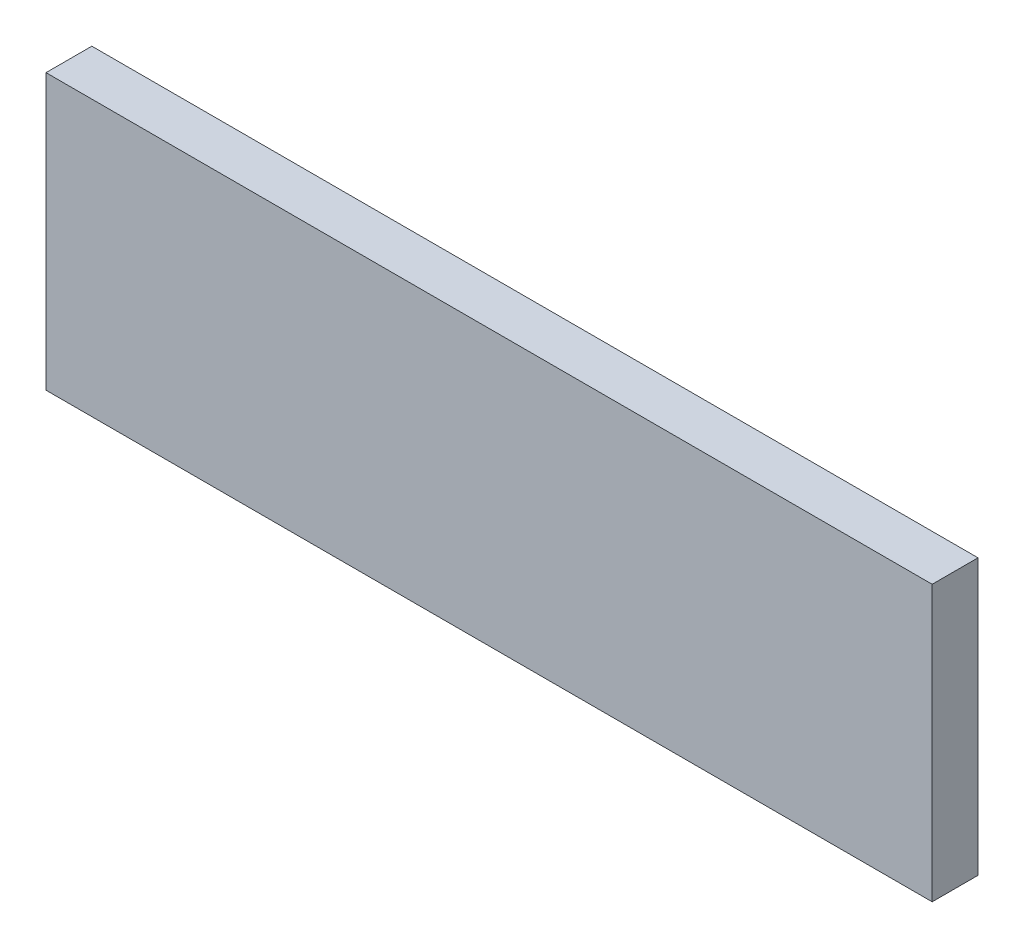
SolidWorks part; units mm, degrees
material "Pine"
ref_plane "Front" through (0, 0, 0) normal (0, 0, 1) x (1, 0, 0)
ref_plane "Top" through (0, 0, 0) normal (0, 1, 0) x (1, 0, 0)
ref_plane "Right" through (0, 0, 0) normal (1, 0, 0) x (0, 0, -1)
sketch "Sketch1" plane through (0, 0, 0) normal (1, 0, 0) x (0, 0, -1)
  line L1 (-9.525, -57.15) -> (9.525, -57.15)
  line L2 (-9.525, -57.15) -> (-9.525, 57.15)
  line L3 (-9.525, 57.15) -> (9.525, 57.15)
  line L4 (9.525, -57.15) -> (9.525, 57.15)
  line L5 (-9.525, -57.15) -> (9.525, 57.15) construction
  line L6 (-9.525, 57.15) -> (9.525, -57.15) construction
  point P0 (0, 0)
  dimension "D1" = 114.3
  dimension "D2" = 19.05
extrude "Boss-Extrude1" add sketch "Sketch1" along normal blind 368.3
